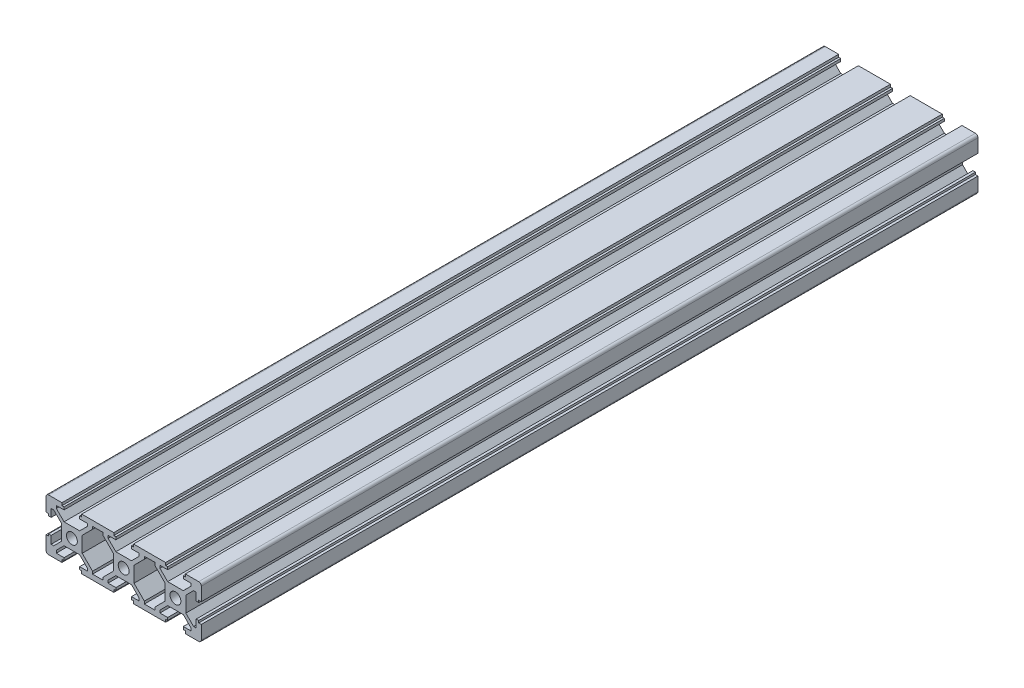
SolidWorks part; units mm, degrees
material "6061 合金"
ref_plane "前视基准面" through (0, 0, 0) normal (0, 0, 1) x (1, 0, 0)
ref_plane "上视基准面" through (0, 0, 0) normal (0, 1, 0) x (1, 0, 0)
ref_plane "右视基准面" through (0, 0, 0) normal (1, 0, 0) x (0, 0, -1)
sketch "草图1" plane through (0, 0, 0) normal (0, 0, 1) x (1, 0, 0)
  line L0 (-32.2486, -0.2298) -> (-32.2486, -1.031)
  line L1 (-32.2486, -1.031) -> (-33.25, -1.031)
  line L2 (-33.25, -1.031) -> (-33.25, -6.2384)
  line L3 (-32.2438, -7.2255) -> (-27.0786, -7.2255)
  line L4 (-27.0786, -7.2255) -> (-27.0786, -6.2241)
  line L5 (-27.0786, -6.2241) -> (-26.2774, -6.2241)
  line L6 (-26.2774, -6.2241) -> (-26.2774, -5.2127)
  line L7 (-26.2774, -5.2127) -> (-29.273, -5.2127)
  line L8 (-29.273, -5.2127) -> (-29.273, -4.2115)
  line L9 (-29.273, -4.2115) -> (-26.2796, -1.2254)
  line L10 (-26.2796, -1.2254) -> (-20.249, -1.2254)
  line L14 (-20.249, -1.2254) -> (-17.2556, -4.2115)
  line L15 (-17.2556, -4.2115) -> (-17.2556, -5.2127)
  line L16 (-17.2556, -5.2127) -> (-20.2513, -5.2127)
  line L17 (-20.2513, -5.2127) -> (-20.2513, -6.2241)
  line L18 (-20.2513, -6.2241) -> (-19.4501, -6.2241)
  line L19 (-19.4501, -6.2241) -> (-19.4501, -7.2255)
  line L20 (-19.4501, -7.2255) -> (-7.0642, -7.2255)
  line L21 (-7.0642, -7.2255) -> (-7.0642, -6.2241)
  line L22 (-7.0642, -6.2241) -> (-6.2631, -6.2241)
  line L23 (-6.2631, -6.2241) -> (-6.2631, -5.2127)
  line L24 (-6.2631, -5.2127) -> (-9.2587, -5.2127)
  line L25 (-9.2587, -5.2127) -> (-9.2587, -4.2115)
  line L26 (-9.2587, -4.2115) -> (-6.2653, -1.2254)
  line L27 (-6.2653, -1.2254) -> (-0.2347, -1.2254)
  line L31 (-0.2347, -1.2254) -> (2.7587, -4.2115)
  line L32 (2.7587, -4.2115) -> (2.7587, -5.2127)
  line L33 (2.7587, -5.2127) -> (-0.2369, -5.2127)
  line L34 (-0.2369, -5.2127) -> (-0.2369, -6.2241)
  line L35 (-0.2369, -6.2241) -> (0.5642, -6.2241)
  line L36 (0.5642, -6.2241) -> (0.5642, -7.2255)
  line L37 (0.5642, -7.2255) -> (12.9455, -7.2255)
  line L38 (12.9455, -7.2255) -> (12.9455, -6.2191)
  line L39 (12.9455, -6.2191) -> (13.7512, -6.2191)
  line L40 (13.7512, -6.2191) -> (13.7512, -5.2127)
  line L41 (13.7512, -5.2127) -> (10.7556, -5.2127)
  line L42 (10.7556, -5.2127) -> (10.7556, -4.2115)
  line L43 (10.7556, -4.2115) -> (13.749, -1.2254)
  line L44 (13.749, -1.2254) -> (19.7796, -1.2254)
  line L48 (19.7796, -1.2254) -> (22.773, -4.2115)
  line L49 (22.773, -4.2115) -> (22.773, -5.2127)
  line L50 (22.773, -5.2127) -> (19.7728, -5.2127)
  line L51 (19.7728, -5.2127) -> (19.7728, -6.2191)
  line L52 (19.7728, -6.2191) -> (20.5739, -6.2191)
  line L53 (20.5739, -6.2191) -> (20.5739, -7.2255)
  line L54 (20.5739, -7.2255) -> (25.7438, -7.2255)
  line L55 (26.75, -6.2384) -> (26.75, -1.031)
  line L56 (26.75, -1.031) -> (25.7485, -1.031)
  line L57 (25.7485, -1.031) -> (25.7485, -0.2298)
  line L58 (25.7485, -0.2298) -> (24.7613, -0.2298)
  line L59 (24.7613, -0.2298) -> (24.7613, -3.2342)
  line L60 (24.7613, -3.2342) -> (23.7599, -3.2342)
  line L61 (23.7599, -3.2342) -> (20.7701, -0.2372)
  line L65 (20.7701, -0.2372) -> (20.7701, 5.7861)
  line L66 (20.7701, 5.7861) -> (23.7599, 8.7832)
  line L67 (23.7599, 8.7832) -> (24.7613, 8.7832)
  line L68 (24.7613, 8.7832) -> (24.7613, 5.7788)
  line L69 (24.7613, 5.7788) -> (25.7485, 5.7788)
  line L70 (25.7485, 5.7788) -> (25.7485, 6.5799)
  line L71 (25.7485, 6.5799) -> (26.75, 6.5799)
  line L72 (26.75, 6.5799) -> (26.75, 11.7682)
  line L73 (25.7438, 12.7745) -> (20.5739, 12.7745)
  line L74 (20.5739, 12.7745) -> (20.5739, 11.7681)
  line L75 (20.5739, 11.7681) -> (19.7728, 11.7681)
  line L76 (19.7728, 11.7681) -> (19.7728, 10.7617)
  line L77 (19.7728, 10.7617) -> (22.773, 10.7617)
  line L78 (22.773, 10.7617) -> (22.773, 9.7604)
  line L79 (22.773, 9.7604) -> (19.7796, 6.7743)
  line L83 (19.7796, 6.7743) -> (13.749, 6.7743)
  line L84 (13.749, 6.7743) -> (10.7556, 9.7604)
  line L85 (10.7556, 9.7604) -> (10.7556, 10.7617)
  line L86 (10.7556, 10.7617) -> (13.7466, 10.7617)
  line L87 (13.7466, 10.7617) -> (13.7466, 11.7681)
  line L88 (13.7466, 11.7681) -> (12.9455, 11.7681)
  line L89 (12.9455, 11.7681) -> (12.9455, 12.7745)
  line L90 (12.9455, 12.7745) -> (0.5642, 12.7745)
  line L91 (0.5642, 12.7745) -> (0.5642, 11.773)
  line L92 (0.5642, 11.773) -> (-0.2369, 11.773)
  line L93 (-0.2369, 11.773) -> (-0.2369, 10.7617)
  line L94 (-0.2369, 10.7617) -> (2.7587, 10.7617)
  line L95 (2.7587, 10.7617) -> (2.7587, 9.7604)
  line L96 (2.7587, 9.7604) -> (-0.2347, 6.7743)
  line L100 (-0.2347, 6.7743) -> (-6.2653, 6.7743)
  line L101 (-6.2653, 6.7743) -> (-9.2587, 9.7604)
  line L102 (-9.2587, 9.7604) -> (-9.2587, 10.7617)
  line L103 (-9.2587, 10.7617) -> (-6.2631, 10.7617)
  line L104 (-6.2631, 10.7617) -> (-6.2631, 11.773)
  line L105 (-6.2631, 11.773) -> (-7.0642, 11.773)
  line L106 (-7.0642, 11.773) -> (-7.0642, 12.7745)
  line L107 (-7.0642, 12.7745) -> (-19.4501, 12.7745)
  line L108 (-19.4501, 12.7745) -> (-19.4501, 11.773)
  line L109 (-19.4501, 11.773) -> (-20.2513, 11.773)
  line L110 (-20.2513, 11.773) -> (-20.2513, 10.7617)
  line L111 (-20.2513, 10.7617) -> (-17.2556, 10.7617)
  line L112 (-17.2556, 10.7617) -> (-17.2556, 9.7604)
  line L113 (-17.2556, 9.7604) -> (-20.249, 6.7743)
  line L117 (-20.249, 6.7743) -> (-26.2796, 6.7743)
  line L118 (-26.2796, 6.7743) -> (-29.273, 9.7604)
  line L119 (-29.273, 9.7604) -> (-29.273, 10.7617)
  line L120 (-29.273, 10.7617) -> (-26.2774, 10.7617)
  line L121 (-26.2774, 10.7617) -> (-26.2774, 11.773)
  line L122 (-26.2774, 11.773) -> (-27.0786, 11.773)
  line L123 (-27.0786, 11.773) -> (-27.0786, 12.7745)
  line L124 (-27.0786, 12.7745) -> (-32.2438, 12.7745)
  line L125 (-33.25, 11.7682) -> (-33.25, 6.5608)
  line L126 (-33.25, 6.5608) -> (-32.2486, 6.5608)
  line L127 (-32.2486, 6.5608) -> (-32.2486, 5.7596)
  line L128 (-32.2486, 5.7596) -> (-31.2613, 5.7596)
  line L129 (-31.2613, 5.7596) -> (-31.2613, 8.764)
  line L130 (-31.2613, 8.764) -> (-30.2599, 8.764)
  line L131 (-30.2599, 8.764) -> (-27.2701, 5.767)
  line L135 (-27.2701, 5.767) -> (-27.2701, -0.2372)
  line L136 (-27.2701, -0.2372) -> (-30.2599, -3.2342)
  line L137 (-30.2599, -3.2342) -> (-31.2613, -3.2342)
  line L138 (-31.2613, -3.2342) -> (-31.2613, -0.2298)
  line L139 (-31.2613, -0.2298) -> (-32.2486, -0.2298)
  line L147 (-19.2585, 5.7861) -> (-19.2585, -0.2372)
  line L150 (-19.2585, -0.2372) -> (-15.2673, -4.2381)
  line L151 (-15.2673, -4.2381) -> (-15.2673, -5.2223)
  line L152 (-15.2673, -5.2223) -> (-11.247, -5.2223)
  line L153 (-11.247, -5.2223) -> (-11.247, -4.2381)
  line L154 (-11.247, -4.2381) -> (-7.2558, -0.2372)
  line L155 (-7.2558, -0.2372) -> (-7.2558, 2.7745)
  line L156 (-7.2558, 2.7745) -> (-7.2558, 5.7861)
  line L157 (-7.2558, 5.7861) -> (-11.247, 9.787)
  line L158 (-11.247, 9.787) -> (-11.247, 10.7712)
  line L159 (-11.247, 10.7712) -> (-15.2673, 10.7712)
  line L160 (-15.2673, 10.7712) -> (-15.2673, 9.787)
  line L161 (-15.2673, 9.787) -> (-19.2585, 5.7861)
  line L162 (4.747, -5.2223) -> (8.7673, -5.2223)
  line L163 (8.7673, -5.2223) -> (8.7673, -4.2381)
  line L164 (8.7673, -4.2381) -> (12.7585, -0.2372)
  line L165 (12.7585, -0.2372) -> (12.7585, 2.7745)
  line L166 (12.7585, 2.7745) -> (12.7585, 5.7861)
  line L167 (12.7585, 5.7861) -> (8.7673, 9.787)
  line L168 (8.7673, 9.787) -> (8.7673, 10.7712)
  line L169 (8.7673, 10.7712) -> (4.747, 10.7712)
  line L170 (4.747, 10.7712) -> (4.747, 9.787)
  line L171 (4.747, 9.787) -> (0.7558, 5.7861)
  line L172 (0.7558, 5.7861) -> (0.7558, 2.7745)
  line L173 (0.7558, 2.7745) -> (0.7558, -0.2372)
  line L174 (0.7558, -0.2372) -> (4.747, -4.2381)
  line L175 (4.747, -4.2381) -> (4.747, -5.2223)
  line L176 (-23.25, 2.7745) -> (-23.25, 12.5158) construction
  line L177 (-23.25, 2.7745) -> (-33.2945, 2.7745) construction
  line L178 (-23.25, 2.7745) -> (-23.25, -7.2784) construction
  line L179 (-23.25, 2.7745) -> (-17.6462, 2.7745) construction
  line L180 (-3.25, 2.7745) -> (-3.25, 12.9074) construction
  line L181 (-3.25, 2.7745) -> (-3.25, -7.2598) construction
  line L182 (-3.25, 2.7745) -> (-8.8035, 2.7745) construction
  line L183 (-3.25, 2.7745) -> (2.4087, 2.7745) construction
  line L184 (16.75, 2.7745) -> (16.75, 12.9038) construction
  line L185 (16.75, 2.7745) -> (26.8187, 2.7745) construction
  line L186 (16.75, 2.7745) -> (16.75, -7.3953) construction
  line L187 (16.75, 2.7745) -> (10.7407, 2.7745) construction
  circle A0 centre (-3.25, 2.7745) radius 2.103
  circle A1 centre (-23.25, 2.7745) radius 2.103
  circle A2 centre (16.75, 2.7745) radius 2.103
  arc A3 (-33.25, -6.2384) -> (-32.2438, -7.2255) centre (-32.2487, -6.2241) ccw
  arc A4 (25.7438, -7.2255) -> (26.75, -6.2384) centre (25.7487, -6.2241) ccw
  arc A5 (26.75, 11.7682) -> (25.7438, 12.7745) centre (25.7486, 11.773) ccw
  arc A6 (-32.2438, 12.7745) -> (-33.25, 11.7682) centre (-32.2486, 11.773) ccw
  point P197 (-29.6612, 12.7745)
  dimension "D1" = 60
  dimension "D2" = 20
  dimension "D3" = 20
  dimension "D4" = 20
  dimension "D5" = 10
  dimension "D6" = 10
  dimension "D7" = 10
  dimension "D8" = 10
extrude "凸台-拉伸1" add sketch "草图1" along normal blind 300
